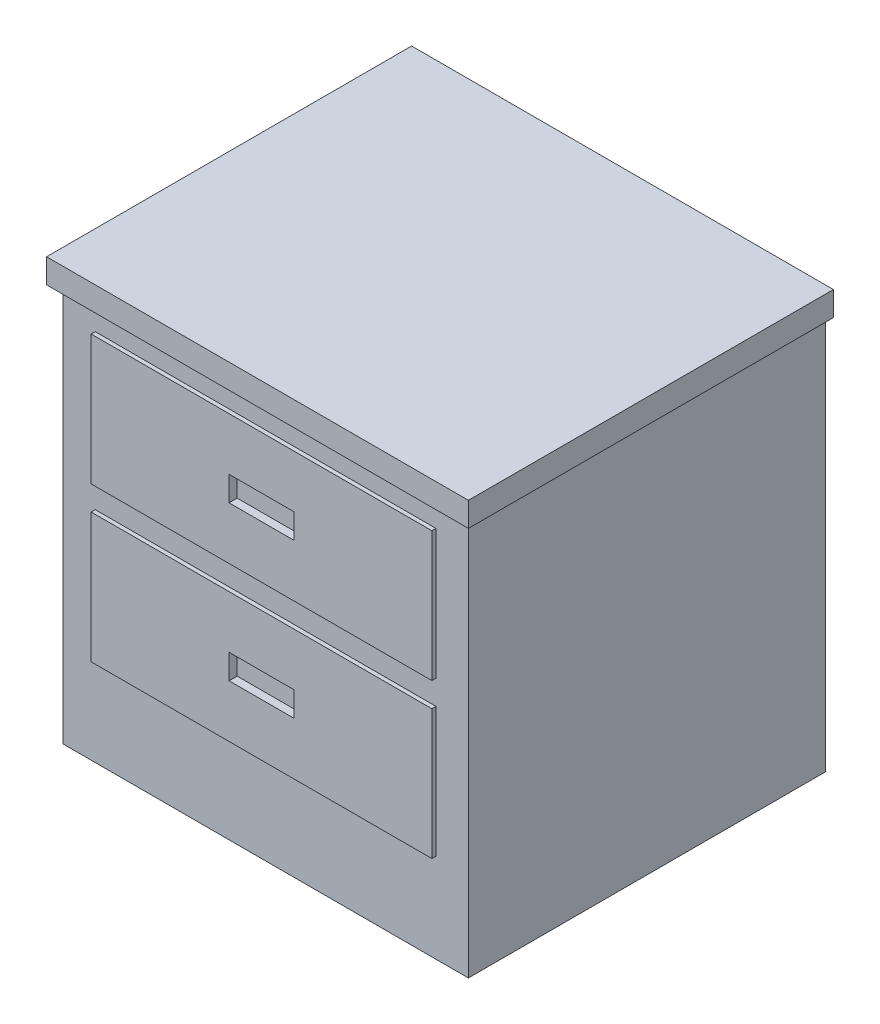
SolidWorks part; units mm, degrees
material "红木"
ref_plane "前视基准面" through (0, 0, 0) normal (0, 0, 1) x (1, 0, 0)
ref_plane "上视基准面" through (0, 0, 0) normal (0, 1, 0) x (1, 0, 0)
ref_plane "右视基准面" through (0, 0, 0) normal (1, 0, 0) x (0, 0, -1)
sketch "草图1" plane through (0, 0, 0) normal (0, 1, 0) x (1, 0, 0)
  line L1 (-250, -220) -> (250, -220)
  line L2 (-250, -220) -> (-250, 220)
  line L3 (-250, 220) -> (250, 220)
  line L4 (250, -220) -> (250, 220)
  line L5 (-250, -220) -> (250, 220) construction
  line L6 (-250, 220) -> (250, -220) construction
  point P0 (0, 0)
  dimension "D1" = 500
  dimension "D2" = 440
extrude "凸台-拉伸1" add sketch "草图1" along normal blind 520
sketch "草图2" plane through (0, 520, 0) normal (0, 1, 0) x (1, 0, 0)
  line L0 (250, 220) -> (-250, 220) construction
  line L1 (-260, -230) -> (260, -230)
  line L2 (-260, -230) -> (-260, 220)
  line L3 (-260, 220) -> (260, 220)
  line L4 (260, -230) -> (260, 220)
  line L5 (-260, -230) -> (260, 220) construction
  line L6 (-260, 220) -> (260, -230) construction
  point P0 (0, -5)
  dimension "D1" = 520
  dimension "D2" = 450
extrude "凸台-拉伸2" add sketch "草图2" against normal blind 30
sketch "草图3" plane through (0, 0, 220) normal (0, 0, 1) x (1, 0, 0)
  line L0 (250, 490) -> (-250, 490) construction
  line L2 (-210, 300) -> (210, 300)
  line L3 (-210, 300) -> (-210, 460)
  line L4 (-210, 460) -> (210, 460)
  line L5 (210, 300) -> (210, 460)
  line L6 (-210, 300) -> (210, 460) construction
  line L7 (-210, 460) -> (210, 300) construction
  point P1 (0, 380)
  dimension "D1" = 420
  dimension "D2" = 30
  dimension "D3" = 160
extrude "凸台-拉伸3" add sketch "草图3" along normal blind 5
sketch "草图4" plane through (0, 0, 225) normal (0, 0, 1) x (1, 0, 0)
  line L0 (-210, 460) -> (210, 300) construction
  line L1 (-40, 364.7619) -> (40, 364.7619)
  line L2 (-40, 364.7619) -> (-40, 395.2381)
  line L3 (-40, 395.2381) -> (40, 395.2381)
  line L4 (40, 364.7619) -> (40, 395.2381)
  line L5 (-40, 364.7619) -> (40, 395.2381) construction
  line L6 (-40, 395.2381) -> (40, 364.7619) construction
  line L7 (-210, 300) -> (210, 460) construction
  point P0 (0, 380)
  dimension "D1" = 80
extrude "切除-拉伸2" cut sketch "草图4" against normal blind 10
pattern_linear "阵列(线性)1" count 2 spacing 190 along (0, -1, 0) of "凸台-拉伸3", "切除-拉伸2"
